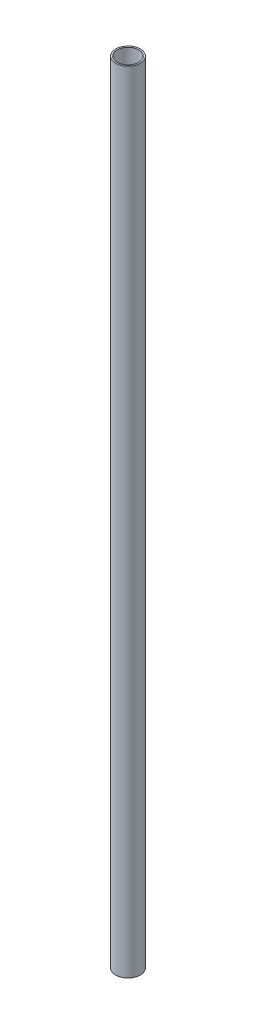
SolidWorks part; units mm, degrees
ref_plane "Front" through (0, 0, 0) normal (0, 0, 1) x (1, 0, 0)
ref_plane "Top" through (0, 0, 0) normal (0, 1, 0) x (1, 0, 0)
ref_plane "Right" through (0, 0, 0) normal (1, 0, 0) x (0, 0, -1)
sketch "Sketch1" plane through (0, 0, 0) normal (0, 1, 0) x (1, 0, 0)
  circle A0 centre (0, 0) radius 12.7
  circle A1 centre (0, 0) radius 11.1125
  dimension "D1" = 25.4
  dimension "D2" = 1.5875
extrude "Extrude1" add sketch "Sketch1" along normal mid plane 812.8
